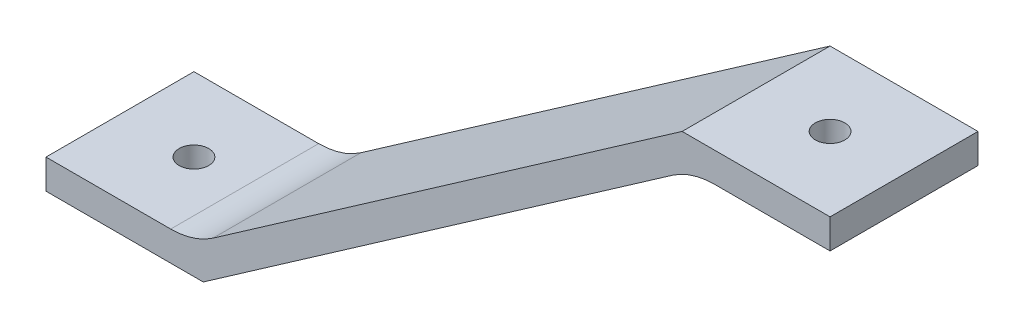
SolidWorks part; units mm, degrees
material "7075-T6 (SN)"
ref_plane "前视基准面" through (0, 0, 0) normal (0, 0, 1) x (1, 0, 0)
ref_plane "上视基准面" through (0, 0, 0) normal (0, 1, 0) x (1, 0, 0)
ref_plane "右视基准面" through (0, 0, 0) normal (1, 0, 0) x (0, 0, -1)
sketch "草图2" plane through (0, 0, 0) normal (0, 0, 1) x (1, 0, 0)
  line L0 (0, 0) -> (0, -4)
  line L1 (0, -4) -> (-18.7436, -4)
  line L2 (-18.7436, -4) -> (-84.7436, -50)
  line L3 (-84.7436, -50) -> (-106, -50)
  line L4 (-106, -50) -> (-106, -46)
  line L5 (-106, -46) -> (-86, -46)
  line L6 (-86, -46) -> (-20, 0)
  line L7 (-20, 0) -> (0, 0)
  dimension "D1" = 4
  dimension "D2" = 4
  dimension "D3" = 4
  dimension "D4" = 20
  dimension "D5" = 20
  dimension "D6" = 50
  dimension "D7" = 106
extrude "凸台-拉伸1" add sketch "草图2" along normal blind 20
sketch "草图3" plane through (0, 0, 0) normal (0, 1, 0) x (1, 0, 0)
  line L0 (0, -10) -> (-5, -10) construction
  line L1 (0, -20) -> (0, 0) construction
  line L2 (-5, -40) -> (-5, 20) construction
  circle A0 centre (-5, 20) radius 1.5
  circle A1 centre (-5, -40) radius 1.5
  point P7 (-5, -10)
  dimension "D2" = 3
  dimension "D1" = 5
  dimension "D3" = 60
sketch "草图6" plane through (0, -46, 0) normal (0, 1, 0) x (1, 0, 0)
  line L0 (-106, -10) -> (-96, -10) construction
  line L1 (-106, -20) -> (-106, 0) construction
  line L2 (-96, -50) -> (-96, 30) construction
  line L3 (-86, 0) -> (-106, 0) construction
  circle A0 centre (-96, 30) radius 1.5
  circle A1 centre (-96, -50) radius 1.5
  point P7 (-96, -10)
  point P9 (-96, 0)
  dimension "D2" = 3
  dimension "D3" = 3
  dimension "D1" = 80
sketch "草图8" plane through (0, -4, 0) normal (0, -1, 0) x (-1, 0, 0)
  line L0 (0, 10) -> (50, 10) construction
  line L1 (0, -20) -> (0, 0) construction
  line L2 (50, 18) -> (50, 2) construction
  circle A0 centre (50, 2) radius 1.5
  circle A1 centre (50, 18) radius 1.5
  point P7 (50, 10)
  point P9 (0, -10)
  dimension "D3" = 3
  dimension "D1" = 16
  dimension "D2" = 50
  dimension "D4" = 20
sketch "草图10" plane through (0, -4, 0) normal (0, -1, 0) x (1, 0, 0)
  line L0 (-50, 50) -> (-50, 30) construction
  line L1 (-50, 40) -> (-26.3, 40) construction
  line L2 (0, 20) -> (0, 0) construction
  circle A0 centre (-50, 50) radius 1.5
  circle A1 centre (-50, 30) radius 1.5
  circle A2 centre (-26.3, 40) radius 1.5
  point P3 (-50, 40)
  point P11 (0, 10)
  dimension "D3" = 3
  dimension "D1" = 20
  dimension "D2" = 23.7
  dimension "D4" = 50
  dimension "D5" = 30
fillet "圆角1" [suppressed] radius 10
extrude "切除-拉伸3" [suppressed] cut sketch "草图8" against normal through all
extrude "切除-拉伸4" [suppressed] cut sketch "草图10" against normal through all
sketch "草图11" plane through (0, 0, 0) normal (0, 1, 0) x (1, 0, 0)
  line L0 (0, -10) -> (-10, -10) construction
  line L1 (0, -20) -> (0, 0) construction
  line L2 (-10, -20) -> (-10, 0) construction
  circle A0 centre (-10, 0) radius 1.5
  circle A1 centre (-10, -20) radius 1.5
  point P7 (-10, -10)
  dimension "D2" = 3
  dimension "D1" = 10
  dimension "D3" = 20
extrude "切除-拉伸5" [suppressed] cut sketch "草图11" against normal through all
sketch "草图12" plane through (0, -46, 0) normal (0, 1, 0) x (1, 0, 0)
  line L0 (-106, -10) -> (-86, -10) construction
  line L1 (-106, -20) -> (-106, 0) construction
  line L2 (-86, 0) -> (-86, -20) construction
  circle A0 centre (-86, 0) radius 2
  circle A1 centre (-86, -20) radius 2
  point P7 (-86, -10)
  dimension "D3" = 4
  dimension "D1" = 20
  dimension "D2" = 20
extrude "切除-拉伸6" [suppressed] cut sketch "草图12" against normal through all
sketch "草图13" plane through (0, 0, 0) normal (0, 1, 0) x (1, 0, 0)
  line L0 (0, -10) -> (-10, -10) construction
  line L1 (0, -20) -> (0, 0) construction
  circle A0 centre (-10, -10) radius 2
  dimension "D1" = 4
  dimension "D2" = 10
extrude "切除-拉伸7" cut sketch "草图13" against normal through all
sketch "草图16" plane through (0, -50, 0) normal (0, -1, 0) x (1, 0, 0)
  line L0 (-106, 10) -> (-96, 10) construction
  line L1 (-106, 20) -> (-106, 0) construction
  circle A0 centre (-96, 10) radius 2
  dimension "D1" = 4
  dimension "D2" = 10
extrude "切除-拉伸8" cut sketch "草图16" against normal through all
fillet "圆角2" radius 10 2 edges at (-18.7436, -4, 10) (-86, -46, 10)
